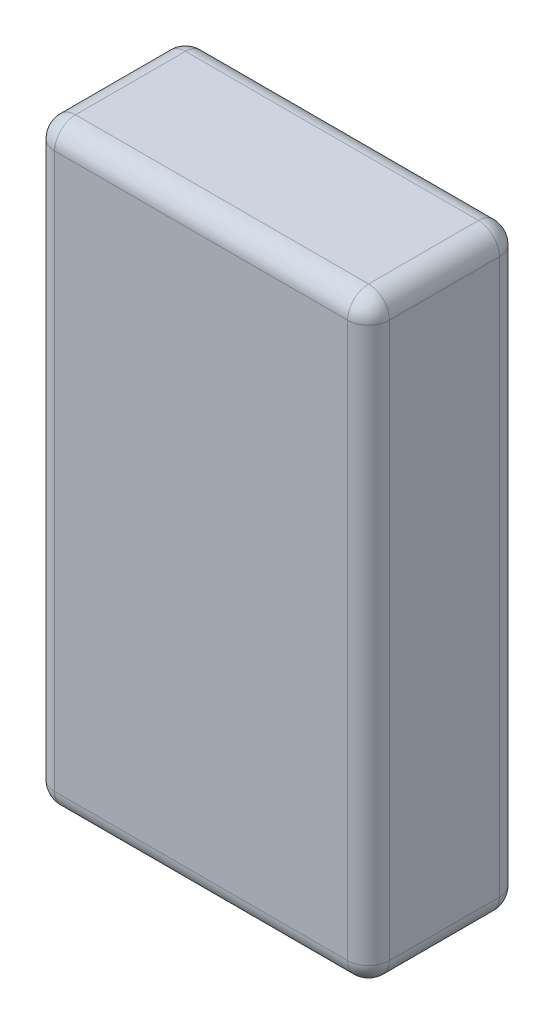
SolidWorks part; units mm, degrees
ref_plane "Front Plane" through (0, 0, 0) normal (0, 0, 1) x (1, 0, 0)
ref_plane "Top Plane" through (0, 0, 0) normal (0, 1, 0) x (1, 0, 0)
ref_plane "Right Plane" through (0, 0, 0) normal (1, 0, 0) x (0, 0, -1)
sketch "Sketch1" plane through (0, 0, 0) normal (0, 1, 0) x (1, 0, 0)
  line L1 (0, 0) -> (32, 0)
  line L2 (0, 0) -> (0, 14.5)
  line L3 (0, 14.5) -> (32, 14.5)
  line L4 (32, 0) -> (32, 14.5)
  dimension "D1" = 14.5
  dimension "D2" = 32
extrude "Boss-Extrude1" add sketch "Sketch1" along normal blind 57
fillet "Fillet1" radius 2 12 edges at (16, 0, 0) (32, 0, -7.25) (0, 57, -7.25) (16, 57, 0) (32, 57, -7.25) (16, 57, -14.5) (32, 28.5, -14.5) (32, 28.5, 0) (0, 28.5, 0) (16, 0, -14.5) (0, 28.5, -14.5) (0, 0, -7.25)
